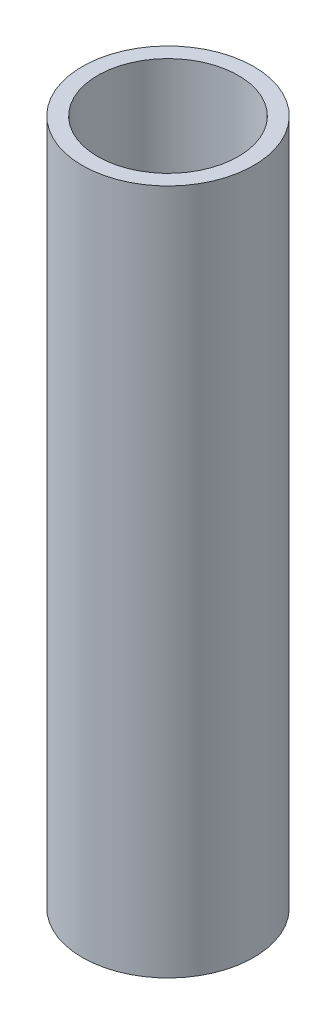
SolidWorks part; units mm, degrees
ref_plane "Front Plane" through (0, 0, 0) normal (0, 0, 1) x (1, 0, 0)
ref_plane "Top Plane" through (0, 0, 0) normal (0, 1, 0) x (1, 0, 0)
ref_plane "Right Plane" through (0, 0, 0) normal (1, 0, 0) x (0, 0, -1)
sketch "Sketch1" plane through (0, 0, 0) normal (0, 1, 0) x (1, 0, 0)
  circle A0 centre (0, 0) radius 12.7
  circle A1 centre (0, 0) radius 10.414
  dimension "D1" = 25.4
  dimension "D2" = 20.828
extrude "Boss-Extrude1" add sketch "Sketch1" along normal blind 101.6
